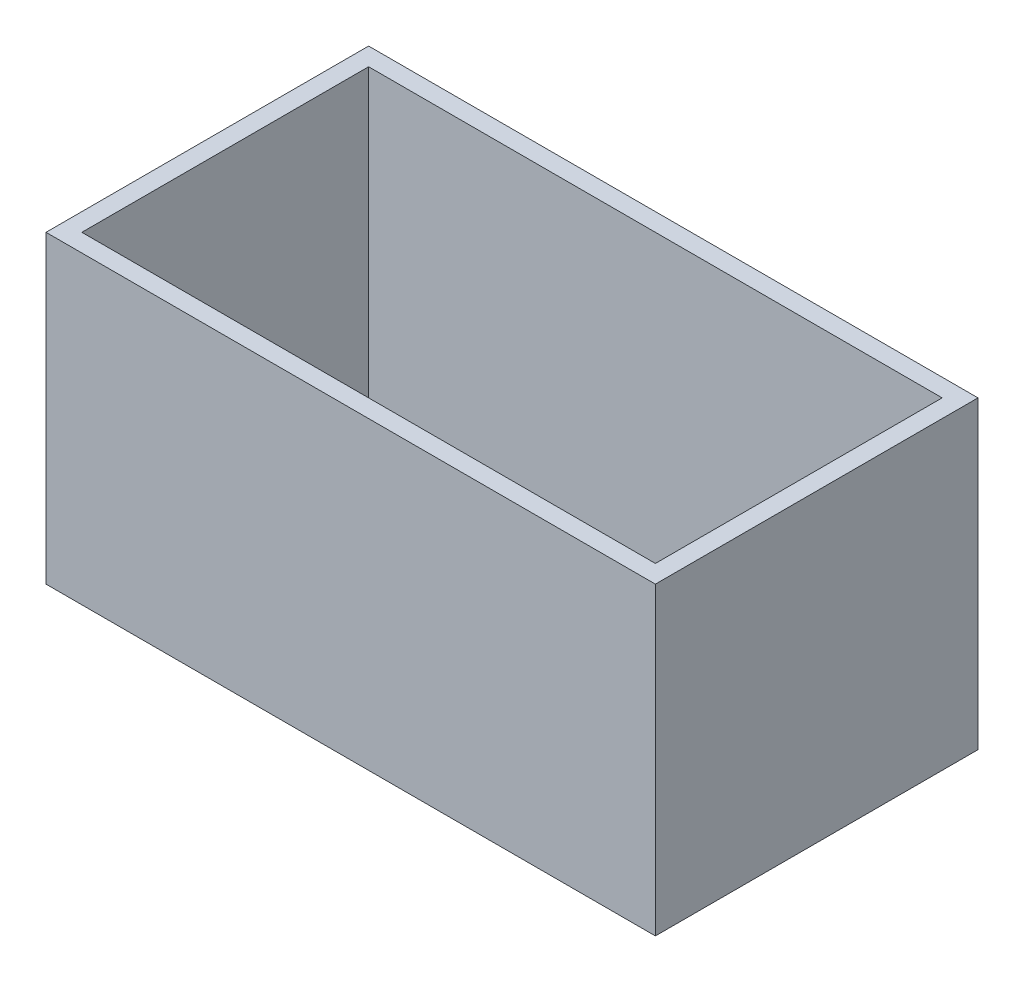
SolidWorks part; units mm, degrees
ref_plane "Front Plane" through (0, 0, 0) normal (0, 0, 1) x (1, 0, 0)
ref_plane "Top Plane" through (0, 0, 0) normal (0, 1, 0) x (1, 0, 0)
ref_plane "Right Plane" through (0, 0, 0) normal (1, 0, 0) x (0, 0, -1)
sketch "Sketch1" plane through (0, 0, 0) normal (0, 1, 0) x (1, 0, 0)
  line L9 (0, 0) -> (609.6, 0)
  line L10 (0, 0) -> (0, 304.8)
  line L11 (0, 304.8) -> (609.6, 304.8)
  line L12 (609.6, 0) -> (609.6, 304.8)
  dimension "D1" = 304.8
  dimension "D2" = 609.6
sketch "Sketch2" plane through (0, 0, 0) normal (0, 1, 0) x (1, 0, 0)
  line L0 (-323.85, 171.45) -> (323.85, -171.45) construction
  line L1 (-323.85, 171.45) -> (323.85, 171.45)
  line L2 (-323.85, 171.45) -> (-323.85, -171.45)
  line L3 (-323.85, -171.45) -> (323.85, -171.45)
  line L4 (323.85, 171.45) -> (323.85, -171.45)
  line L5 (323.85, 171.45) -> (-323.85, -171.45) construction
  point P4 (0, 0)
  dimension "D1" = 647.7
  dimension "D2" = 342.9
extrude "Boss-Extrude1" add sketch "Sketch2" along normal blind 323.85 contours L2 L1 L4 L3
shell "Shell1" thickness 19.05
